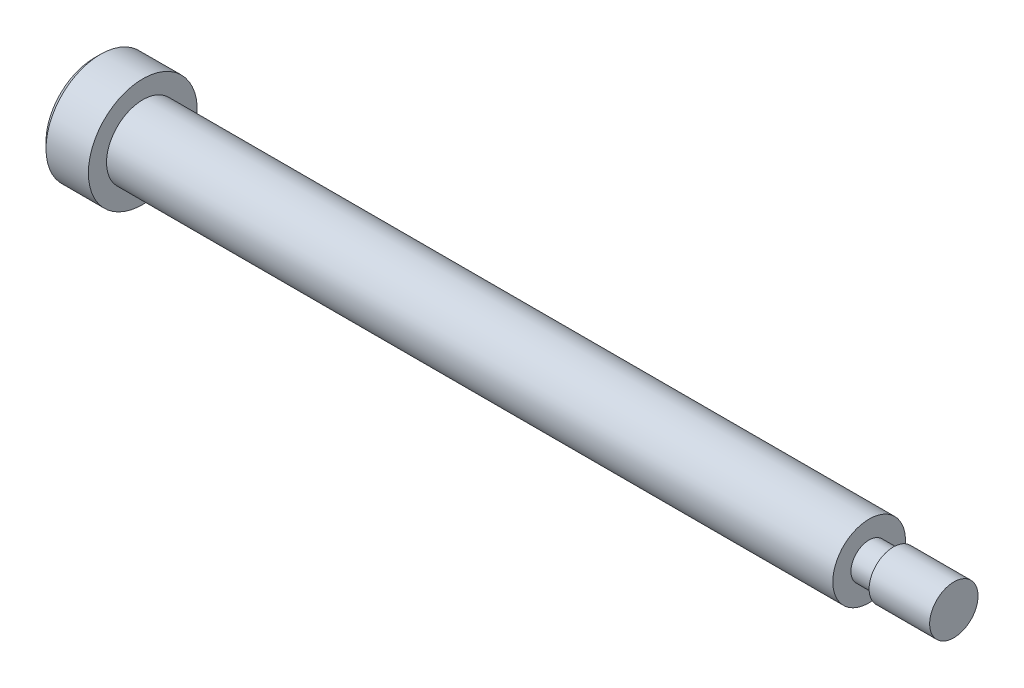
SolidWorks part; units mm, degrees
material "Plain Carbon Steel"
ref_plane "Front Plane" through (0, 0, 0) normal (0, 0, 1) x (1, 0, 0)
ref_plane "Top Plane" through (0, 0, 0) normal (0, 1, 0) x (1, 0, 0)
ref_plane "Right Plane" through (0, 0, 0) normal (1, 0, 0) x (0, 0, -1)
sketch "Sketch1" plane through (0, 0, 0) normal (0, 0, 1) x (1, 0, 0)
  line L0 (0, 3) -> (60, 3)
  line L1 (60, 3) -> (60, 1.5)
  line L2 (60, 1.5) -> (62, 1.5)
  line L3 (62, 1.5) -> (62, 2)
  line L4 (62, 2) -> (67, 2)
  line L5 (67, 2) -> (67, 0)
  line L6 (67, 0) -> (-4, 0)
  line L7 (-4, 0) -> (-4, 4.5)
  line L8 (-4, 4.5) -> (0, 4.5)
  line L9 (0, 4.5) -> (0, 3)
  line L10 (-15.4482, 0) -> (78.4971, 0) construction
  dimension "D1" = 4
  dimension "D2" = 6
  dimension "D3" = 60
  dimension "D4" = 3
  dimension "D5" = 7
  dimension "D6" = 2
  dimension "D7" = 9
  dimension "D8" = 4
revolve "Revolve1" add sketch "Sketch1" angle 360 about L10
cosmetic thread "Cosmetic Thread1" parameters "D2"=3.22
chamfer "Chamfer2" distance 0.5 angle 45 1 edges at (-4, 0, 4.5)
sketch "Sketch2" plane through (-4, 0, 0) normal (-1, 0, 0) x (0, 0, 1)
  line L0 (0, 0) -> (0, 1.7321) construction
  line L1 (0, 1.7321) -> (-1.5, 0.866)
  line L2 (-1.5, 0.866) -> (-1.5, -0.866)
  line L3 (-1.5, -0.866) -> (0, -1.7321)
  line L4 (0, -1.7321) -> (1.5, -0.866)
  line L5 (1.5, -0.866) -> (1.5, 0.866)
  line L6 (1.5, 0.866) -> (0, 1.7321)
  line L7 (0, 1.7321) -> (0.0181, 1.7917) construction
  circle A0 centre (0, 0) radius 1.5 construction
  dimension "D1" = 3
extrude "Cut-Extrude1" cut sketch "Sketch2" against normal blind 2
